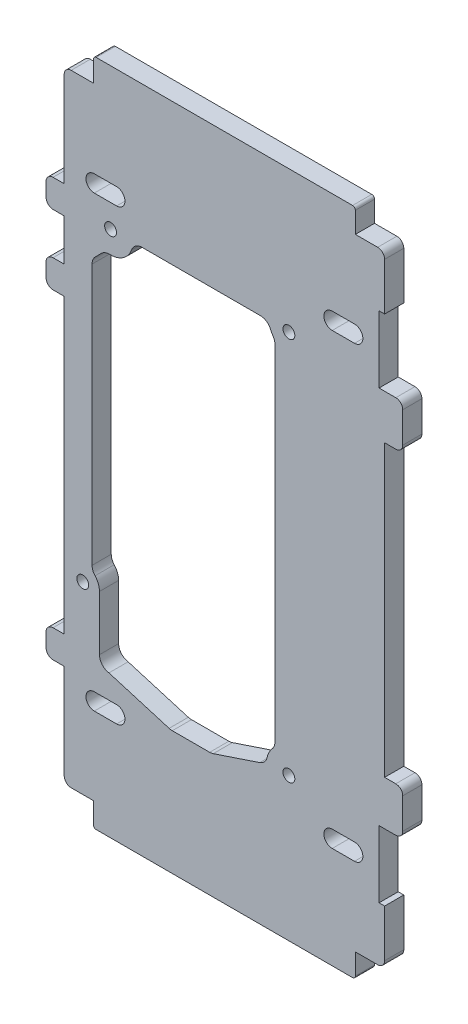
SolidWorks part; units mm, degrees
ref_plane "Front Plane" through (0, 0, 0) normal (0, 0, 1) x (1, 0, 0)
ref_plane "Top Plane" through (0, 0, 0) normal (0, 1, 0) x (1, 0, 0)
ref_plane "Right Plane" through (0, 0, 0) normal (1, 0, 0) x (0, 0, -1)
sketch "Sketch1" plane through (0, 0, 0) normal (0, 0, 1) x (1, 0, 0)
  line L9 (17.8279, -45.2789) -> (25.8279, -45.2789)
  line L10 (25.8279, -51.2789) -> (17.8279, -51.2789)
  line L11 (-65.7048, -13.1789) -> (-65.7048, -32.8247)
  line L12 (-40.7094, -43.2203) -> (-62.3085, -36.7789)
  line L13 (-26.1513, -43.3872) -> (-39.5662, -43.3872)
  line L14 (-8.1769, -37.6018) -> (-24.8843, -43.1812)
  line L15 (-2.7226, -28.4416) -> (-2.7226, 95.0966)
  line L16 (-7.9696, 101.4211) -> (-50.4089, 101.4211)
  line L17 (-65.0095, 92.2583) -> (-67.1932, 90.0746)
  line L18 (-68.3648, -6.3874) -> (-68.3648, 87.2462)
  line L19 (-67.5575, 109.7211) -> (-59.5575, 109.7211)
  line L20 (-59.5575, 115.7211) -> (-67.5575, 115.7211)
  line L21 (17.8279, 109.7211) -> (25.8279, 109.7211)
  line L22 (25.8279, 115.7211) -> (17.8279, 115.7211)
  line L23 (-67.5575, -45.2789) -> (-59.5575, -45.2789)
  line L24 (-59.5575, -51.2789) -> (-67.5575, -51.2789)
  line L25 (-78.3648, -42.7789) -> (-82.3648, -42.7789)
  line L26 (-84.8648, -40.2789) -> (-84.8648, -35.2789)
  line L27 (-82.3648, -32.7789) -> (-78.3648, -32.7789)
  line L28 (-78.3648, 72.2211) -> (-78.3648, -32.7789)
  line L29 (-82.3648, 72.2211) -> (-78.3648, 72.2211)
  line L30 (-84.8648, 79.7211) -> (-84.8648, 74.7211)
  line L31 (-78.3648, 82.2211) -> (-82.3648, 82.2211)
  line L32 (-78.3648, 97.2211) -> (-78.3648, 82.2211)
  line L33 (-82.3648, 97.2211) -> (-78.3648, 97.2211)
  line L34 (-84.8648, 104.7211) -> (-84.8648, 99.7211)
  line L35 (-78.3648, 107.2211) -> (-82.3648, 107.2211)
  line L36 (40.6352, 100.2211) -> (34.6352, 100.2211)
  line L37 (43.1352, 86.7211) -> (43.1352, 97.7211)
  line L38 (36.6352, 84.2211) -> (40.6352, 84.2211)
  line L39 (36.6352, -19.7789) -> (36.6352, 84.2211)
  line L40 (36.6352, -19.7789) -> (40.6352, -19.7789)
  line L41 (43.1352, -22.2789) -> (43.1352, -33.2789)
  line L42 (40.6352, -35.7789) -> (34.6352, -35.7789)
  line L43 (26.1352, -79.2789) -> (34.1352, -79.2789)
  line L44 (26.1352, -79.2789) -> (26.1352, -86.7789)
  line L45 (25.1352, -87.7789) -> (-66.8648, -87.7789)
  line L46 (-67.8648, -86.7789) -> (-67.8648, -79.2789)
  line L47 (-75.8648, -79.2789) -> (-67.8648, -79.2789)
  line L48 (-67.8648, 143.7211) -> (-75.8648, 143.7211)
  line L49 (-67.8648, 151.2211) -> (-67.8648, 143.7211)
  line L50 (25.1352, 152.2211) -> (-66.8648, 152.2211)
  line L51 (26.1352, 143.7211) -> (26.1352, 151.2211)
  line L52 (34.1352, 143.7211) -> (26.1352, 143.7211)
  line L53 (36.6352, 124.2211) -> (36.6352, 141.2211)
  line L54 (-78.3648, 141.2211) -> (-78.3648, 107.2211)
  line L55 (-78.3648, -42.7789) -> (-78.3648, -76.7789)
  line L56 (36.6352, -76.7789) -> (36.6352, -59.7789)
  line L57 (36.6352, -59.7789) -> (34.6352, -59.7789)
  line L58 (34.6352, -59.7789) -> (34.6352, -35.7789)
  line L59 (36.6352, 124.2211) -> (34.6352, 124.2211)
  line L60 (34.6352, 124.2211) -> (34.6352, 100.2211)
  circle A2 centre (-71.7048, -13.1789) radius 2.125
  circle A3 centre (2.2774, 101.4211) radius 2.125
  circle A4 centre (-61.7226, 101.4211) radius 2.125
  circle A5 centre (2.2774, -36.3789) radius 2.125
  arc A6 (25.8279, -51.2789) -> (25.8279, -45.2789) centre (25.8279, -48.2789) ccw
  arc A7 (17.8279, -45.2789) -> (17.8279, -51.2789) centre (17.8279, -48.2789) ccw
  arc A8 (-65.7048, -32.8247) -> (-62.3085, -36.7789) centre (-61.7048, -32.8247) ccw
  arc A9 (-40.7094, -43.2203) -> (-39.5662, -43.3872) centre (-39.5662, -39.3872) ccw
  arc A10 (-26.1513, -43.3872) -> (-24.8843, -43.1812) centre (-26.1513, -39.3872) ccw
  arc A11 (-8.1769, -37.6018) -> (-5.5368, -34.6648) centre (-9.4439, -33.8078) ccw
  arc A12 (-3.7226, -31.0874) -> (-5.5368, -34.6648) centre (2.2774, -36.3789) ccw
  arc A13 (-3.7226, -31.0874) -> (-2.7226, -28.4416) centre (-6.7226, -28.4416) ccw
  arc A14 (-2.7226, 95.0966) -> (-3.4499, 97.3964) centre (-6.7226, 95.0966) ccw
  arc A15 (-4.2434, 98.8757) -> (-3.4499, 97.3964) centre (2.2774, 101.4211) ccw
  arc A16 (-4.2434, 98.8757) -> (-7.9696, 101.4211) centre (-7.9696, 97.4211) ccw
  arc A17 (-50.4089, 101.4211) -> (-54.1801, 98.7545) centre (-50.4089, 97.4211) ccw
  arc A18 (-62.0283, 93.427) -> (-54.1801, 98.7545) centre (-61.7226, 101.4211) ccw
  arc A19 (-62.0283, 93.427) -> (-65.0095, 92.2583) centre (-62.1811, 89.4299) ccw
  arc A20 (-67.1932, 90.0746) -> (-68.3648, 87.2462) centre (-64.3648, 87.2462) ccw
  arc A21 (-68.3648, -6.3874) -> (-67.3008, -9.104) centre (-64.3648, -6.3874) ccw
  arc A22 (-65.7048, -13.1789) -> (-67.3008, -9.104) centre (-71.7048, -13.1789) ccw
  arc A23 (-59.5575, 109.7211) -> (-59.5575, 115.7211) centre (-59.5575, 112.7211) ccw
  arc A24 (-67.5575, 115.7211) -> (-67.5575, 109.7211) centre (-67.5575, 112.7211) ccw
  arc A25 (25.8279, 109.7211) -> (25.8279, 115.7211) centre (25.8279, 112.7211) ccw
  arc A26 (17.8279, 115.7211) -> (17.8279, 109.7211) centre (17.8279, 112.7211) ccw
  arc A27 (-59.5575, -51.2789) -> (-59.5575, -45.2789) centre (-59.5575, -48.2789) ccw
  arc A28 (-67.5575, -45.2789) -> (-67.5575, -51.2789) centre (-67.5575, -48.2789) ccw
  arc A29 (-84.8648, -40.2789) -> (-82.3648, -42.7789) centre (-82.3648, -40.2789) ccw
  arc A30 (-82.3648, -32.7789) -> (-84.8648, -35.2789) centre (-82.3648, -35.2789) ccw
  arc A31 (-84.8648, 74.7211) -> (-82.3648, 72.2211) centre (-82.3648, 74.7211) ccw
  arc A32 (-82.3648, 82.2211) -> (-84.8648, 79.7211) centre (-82.3648, 79.7211) ccw
  arc A33 (-84.8648, 99.7211) -> (-82.3648, 97.2211) centre (-82.3648, 99.7211) ccw
  arc A34 (-82.3648, 107.2211) -> (-84.8648, 104.7211) centre (-82.3648, 104.7211) ccw
  arc A35 (43.1352, 97.7211) -> (40.6352, 100.2211) centre (40.6352, 97.7211) ccw
  arc A36 (40.6352, 84.2211) -> (43.1352, 86.7211) centre (40.6352, 86.7211) ccw
  arc A37 (43.1352, -22.2789) -> (40.6352, -19.7789) centre (40.6352, -22.2789) ccw
  arc A38 (40.6352, -35.7789) -> (43.1352, -33.2789) centre (40.6352, -33.2789) ccw
  arc A39 (25.1352, -87.7789) -> (26.1352, -86.7789) centre (25.1352, -86.7789) ccw
  arc A40 (-67.8648, -86.7789) -> (-66.8648, -87.7789) centre (-66.8648, -86.7789) ccw
  arc A41 (-66.8648, 152.2211) -> (-67.8648, 151.2211) centre (-66.8648, 151.2211) ccw
  arc A42 (26.1352, 151.2211) -> (25.1352, 152.2211) centre (25.1352, 151.2211) ccw
  arc A43 (36.6352, 141.2211) -> (34.1352, 143.7211) centre (34.1352, 141.2211) ccw
  arc A44 (-75.8648, 143.7211) -> (-78.3648, 141.2211) centre (-75.8648, 141.2211) ccw
  arc A45 (-78.3648, -76.7789) -> (-75.8648, -79.2789) centre (-75.8648, -76.7789) ccw
  arc A46 (34.1352, -79.2789) -> (36.6352, -76.7789) centre (34.1352, -76.7789) ccw
extrude "Boss-Extrude1" add sketch "Sketch1" along normal blind 6.88
